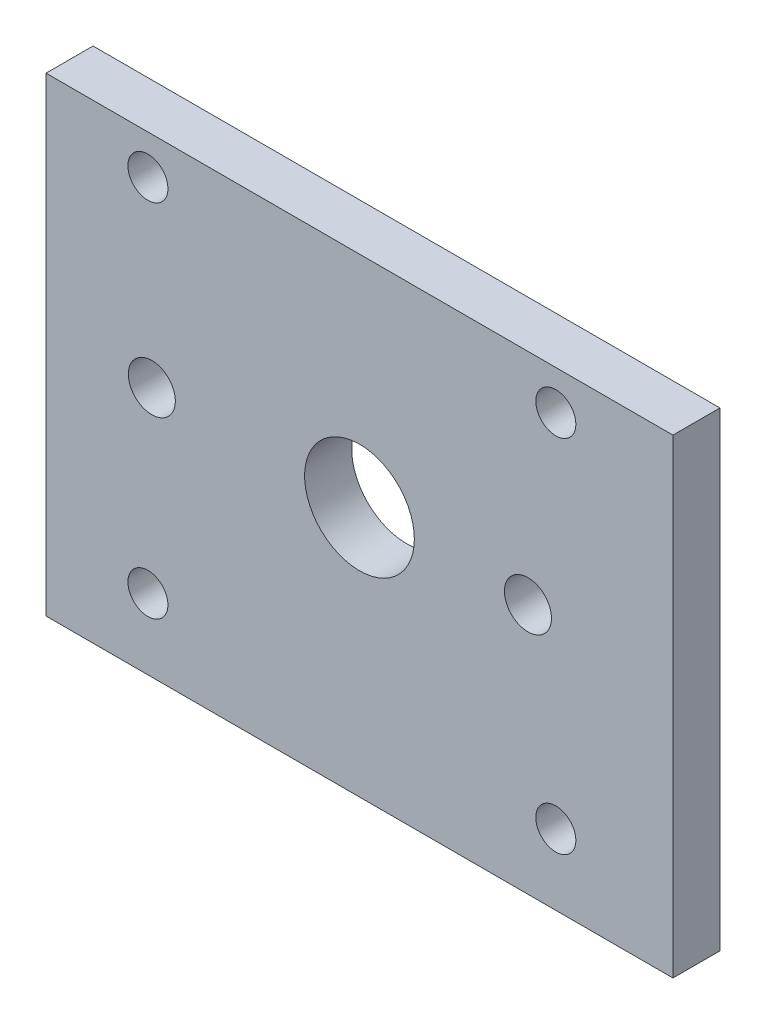
SolidWorks part; units mm, degrees
ref_plane "Front" through (0, 0, 0) normal (0, 0, 1) x (1, 0, 0)
ref_plane "Top" through (0, 0, 0) normal (0, 1, 0) x (1, 0, 0)
ref_plane "Right" through (0, 0, 0) normal (1, 0, 0) x (0, 0, -1)
sketch "草图1" plane through (0, 0, 0) normal (0, 0, 1) x (1, 0, 0)
  line L0 (40, 35) -> (40, -35) construction
  line L1 (-40, 35) -> (40, 35) construction
  line L2 (-40, -35) -> (-40, 35) construction
  line L3 (40, 35) -> (40, -25)
  line L4 (-40, 35) -> (40, 35)
  line L5 (-40, -25) -> (-40, 35)
  line L6 (-40, -25) -> (40, -25)
  circle A9 centre (0, 7) radius 7
  dimension "D2" = 60
extrude "凸台-拉伸1" add sketch "草图1" along normal blind 6
sketch "草图2" plane through (0, 0, 0) normal (0, 0, -1) x (-1, 0, 0)
  line L0 (-40, 35) -> (40, 35) construction
  line L1 (40, 35) -> (40, -25) construction
  circle A0 centre (-21.5, 7) radius 3 construction
  circle A1 centre (26.5, 7) radius 3 construction
  circle A2 centre (-21.5, 7) radius 3
  circle A3 centre (26.5, 7) radius 3
  circle A4 centre (27, 30) radius 2.5551
  circle A5 centre (27, -16) radius 2.5551
  circle A6 centre (-25.0526, -16) radius 2.5551
  circle A7 centre (-25.0526, 30) radius 2.5551
  point P18 (0, 0)
  point P19 (0, 0)
  point P20 (0, 0)
  point P21 (0, 0)
  dimension "D1" = 5
  dimension "D2" = 13
  dimension "D3" = 46
extrude "切除-拉伸1" cut sketch "草图2" against normal blind 10
